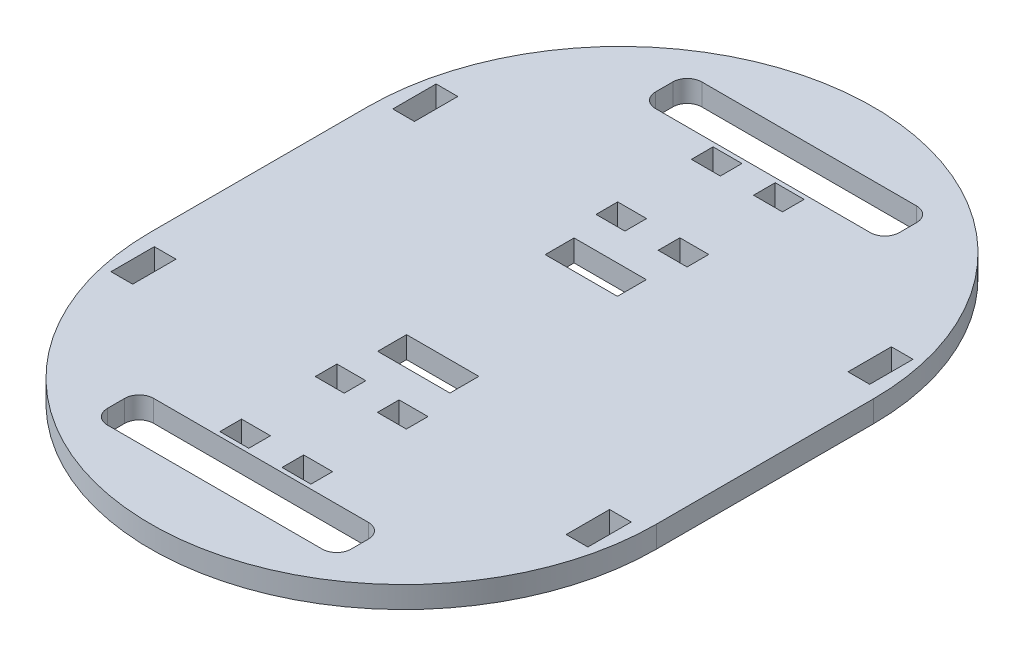
SolidWorks part; units mm, degrees
ref_plane "Front Plane" through (0, 0, 0) normal (0, 0, 1) x (1, 0, 0)
ref_plane "Top Plane" through (0, 0, 0) normal (0, 1, 0) x (1, 0, 0)
ref_plane "Right Plane" through (0, 0, 0) normal (1, 0, 0) x (0, 0, -1)
sketch "Sketch1" plane through (0, 0, 0) normal (0, 1, 0) x (1, 0, 0)
  line L0 (0, 0) -> (0, 76.2) construction
  line L1 (-88.9, 0) -> (-88.9, 76.2)
  line L2 (88.9, 0) -> (88.9, 76.2)
  arc A0 (-88.9, 0) -> (88.9, 0) centre (0, 0) ccw
  arc A1 (88.9, 76.2) -> (-88.9, 76.2) centre (0, 76.2) ccw
  point P3 (0, 38.1)
  dimension "D2" = 88.9
  dimension "D1" = 76.2
extrude "Boss-Extrude1" add sketch "Sketch1" along normal blind 7.62 contours A1 L1 A0 L2
sketch "Sketch2" plane through (0, 7.62, 0) normal (0, 1, 0) x (1, 0, 0)
  line L0 (0, 165.1) -> (0, -88.9) construction
  line L1 (-67.1704, 134.4352) -> (67.1704, 134.4352) construction
  line L3 (-67.1704, -58.2352) -> (67.1704, -58.2352) construction
  line L4 (-42.8387, -66.3632) -> (42.8387, -66.3632)
  line L5 (-42.8387, -66.3632) -> (-42.8387, -50.1072)
  line L6 (-42.8387, -50.1072) -> (42.8387, -50.1072)
  line L7 (42.8387, -66.3632) -> (42.8387, -50.1072)
  line L8 (-42.8387, -66.3632) -> (42.8387, -50.1072) construction
  line L9 (-42.8387, -50.1072) -> (42.8387, -66.3632) construction
  line L15 (-88.9, 38.1) -> (88.9, 38.1) construction
  line L16 (-88.9, 0) -> (-88.9, 76.2) construction
  line L17 (88.9, 0) -> (88.9, 76.2) construction
  line L18 (-42.8387, 142.5632) -> (42.8387, 126.3072) construction
  line L19 (-67.1704, 134.4352) -> (67.1704, 134.4352) construction
  line L20 (-42.8387, 126.3072) -> (42.8387, 142.5632) construction
  line L21 (42.8387, 142.5632) -> (42.8387, 126.3072)
  line L22 (-42.8387, 126.3072) -> (42.8387, 126.3072)
  line L23 (-42.8387, 142.5632) -> (-42.8387, 126.3072)
  line L24 (-42.8387, 142.5632) -> (42.8387, 142.5632)
  arc A0 (88.9, 76.2) -> (-88.9, 76.2) centre (0, 76.2) ccw construction
  arc A1 (-88.9, 0) -> (88.9, 0) centre (0, 0) ccw construction
  point P10 (0, -58.2352)
  dimension "D1" = 16.256
extrude "Cut-Extrude1" cut sketch "Sketch2" against normal through all and the other way through all contours L6 L7 L4 L5 | L22 L21 L24 L23
fillet "Fillet1" radius 5.08 8 edges at (-42.8387, 3.81, -142.5632) (-42.8387, 3.81, -126.3072) (42.8387, 3.81, -142.5632) (42.8387, 3.81, -126.3072) (42.8387, 3.81, 50.1072) (42.8387, 3.81, 66.3632) (-42.8387, 3.81, 66.3632) (-42.8387, 3.81, 50.1072)
sketch "Sketch3" plane through (0, 7.62, 0) normal (0, 1, 0) x (1, 0, 0)
  line L0 (-42.8387, 134.4352) -> (42.8387, 134.4352) construction
  line L1 (-42.8387, 137.4832) -> (-42.8387, 131.3872) construction
  line L2 (42.8387, 137.4832) -> (42.8387, 131.3872) construction
  line L3 (0, 134.4352) -> (0, 83.6352) construction
  line L4 (-16.002, 83.6352) -> (16.002, 83.6352)
  line L5 (16.002, 91.2552) -> (16.002, 134.4352) construction
  line L10 (-16.002, 83.6352) -> (-5.842, 83.6352)
  line L11 (-16.002, 83.6352) -> (-16.002, 91.2552)
  line L12 (-16.002, 91.2552) -> (-5.842, 91.2552)
  line L13 (-5.842, 83.6352) -> (-5.842, 91.2552)
  line L14 (16.002, 83.6352) -> (5.842, 83.6352)
  line L15 (16.002, 83.6352) -> (16.002, 91.2552)
  line L16 (16.002, 91.2552) -> (5.842, 91.2552)
  line L17 (5.842, 83.6352) -> (5.842, 91.2552)
  line L18 (-16.002, 91.2552) -> (-16.002, 134.4352) construction
  line L19 (16.002, 134.4352) -> (16.002, 124.7832) construction
  line L20 (16.002, 117.1632) -> (-16.002, 117.1632) construction
  line L21 (16.002, 124.7832) -> (5.842, 124.7832)
  line L22 (16.002, 124.7832) -> (16.002, 117.1632)
  line L23 (16.002, 117.1632) -> (5.842, 117.1632)
  line L24 (5.842, 124.7832) -> (5.842, 117.1632)
  line L25 (-16.002, 124.7832) -> (-5.842, 124.7832)
  line L26 (-16.002, 124.7832) -> (-16.002, 117.1632)
  line L27 (-16.002, 117.1632) -> (-5.842, 117.1632)
  line L28 (-5.842, 124.7832) -> (-5.842, 117.1632)
  line L29 (-88.9, 38.1) -> (88.9, 38.1) construction
  line L30 (-88.9, 0) -> (-88.9, 76.2) construction
  line L31 (88.9, 0) -> (88.9, 76.2) construction
  line L32 (16.002, -15.0552) -> (5.842, -15.0552)
  line L33 (5.842, -7.4352) -> (5.842, -15.0552)
  line L34 (16.002, -7.4352) -> (5.842, -7.4352)
  line L35 (16.002, -7.4352) -> (16.002, -15.0552)
  line L36 (-16.002, -15.0552) -> (-5.842, -15.0552)
  line L37 (-5.842, -7.4352) -> (-5.842, -15.0552)
  line L38 (-16.002, -7.4352) -> (-5.842, -7.4352)
  line L39 (-16.002, -7.4352) -> (-16.002, -15.0552)
  line L40 (16.002, -40.9632) -> (5.842, -40.9632)
  line L41 (5.842, -48.5832) -> (5.842, -40.9632)
  line L42 (16.002, -48.5832) -> (5.842, -48.5832)
  line L43 (16.002, -48.5832) -> (16.002, -40.9632)
  line L44 (-16.002, -40.9632) -> (-5.842, -40.9632)
  line L45 (-5.842, -48.5832) -> (-5.842, -40.9632)
  line L46 (-16.002, -48.5832) -> (-5.842, -48.5832)
  line L47 (-16.002, -48.5832) -> (-16.002, -40.9632)
  line L48 (42.8387, -58.2352) -> (-42.8387, -58.2352) construction
  line L49 (42.8387, -61.2832) -> (42.8387, -55.1872) construction
  line L50 (-42.8387, -61.2832) -> (-42.8387, -55.1872) construction
  point P12 (0, 83.6352)
  dimension "D1" = 50.8
  dimension "D2" = 32.004
  dimension "D3" = 7.62
  dimension "D4" = 7.62
  dimension "D5" = 9.652
  dimension "D6" = 7.62
  dimension "D7" = 7.62
  dimension "D8" = 0
  dimension "D9" = 9.652
extrude "Cut-Extrude2" cut sketch "Sketch3" against normal through all contours L17 L4 L15 L16 | L4 L13 L12 L11 | L22 L21 L24 L23 | L26 L25 L28 L27 | L36 L37 L38 L39 | L32 L33 L34 L35 | L44 L45 L46 L47 | L40 L41 L42 L43
sketch "Sketch4" plane through (0, 7.62, 0) normal (0, 1, 0) x (1, 0, 0)
  line L0 (-5.842, 83.6352) -> (5.842, 83.6352) construction
  line L1 (5.842, 83.6352) -> (5.842, 73.4752) construction
  line L2 (-12.7, 62.4579) -> (-12.7, 72.6179)
  line L3 (0, 83.6352) -> (0, 67.5379) construction
  line L4 (-12.7, 62.4579) -> (12.7, 62.4579)
  line L5 (-12.7, 72.6179) -> (12.7, 72.6179)
  line L6 (12.7, 62.4579) -> (12.7, 72.6179)
  line L7 (-12.7, 62.4579) -> (12.7, 72.6179) construction
  line L8 (-12.7, 72.6179) -> (12.7, 62.4579) construction
  line L11 (-88.9, 38.1) -> (88.9, 38.1) construction
  line L12 (-88.9, 0) -> (-88.9, 76.2) construction
  line L13 (88.9, 0) -> (88.9, 76.2) construction
  line L14 (-12.7, 13.7421) -> (12.7, 13.7421)
  line L15 (-12.7, 13.7421) -> (-12.7, 3.5821)
  line L16 (-12.7, 3.5821) -> (12.7, 3.5821)
  line L17 (12.7, 13.7421) -> (12.7, 3.5821)
  dimension "D1" = 10.16
  dimension "D2" = 10.16
  dimension "D3" = 25.4
extrude "Cut-Extrude3" cut sketch "Sketch4" against normal through all
sketch "Sketch5" plane through (0, 7.62, 0) normal (0, 1, 0) x (1, 0, 0)
  line L0 (-88.9, 38.1) -> (88.9, 38.1) construction
  line L1 (-88.9, 0) -> (-88.9, 76.2) construction
  line L2 (88.9, 0) -> (88.9, 76.2) construction
  line L3 (0, 165.1) -> (0, -88.9) construction
  line L4 (-83.82, 95.25) -> (-83.82, -19.05) construction
  line L5 (83.82, -3.81) -> (76.2, -3.81)
  line L6 (-83.82, -19.05) -> (-76.2, -19.05)
  line L7 (-83.82, -19.05) -> (-83.82, -3.81)
  line L8 (-83.82, -3.81) -> (-76.2, -3.81)
  line L9 (-76.2, -19.05) -> (-76.2, -3.81)
  line L10 (-83.82, 95.25) -> (-76.2, 95.25)
  line L11 (-83.82, 95.25) -> (-83.82, 80.01)
  line L12 (-83.82, 80.01) -> (-76.2, 80.01)
  line L13 (-76.2, 95.25) -> (-76.2, 80.01)
  line L14 (76.2, -19.05) -> (76.2, -3.81)
  line L15 (83.82, -19.05) -> (76.2, -19.05)
  line L16 (83.82, -19.05) -> (83.82, -3.81)
  line L17 (83.82, 80.01) -> (76.2, 80.01)
  line L18 (76.2, 95.25) -> (76.2, 80.01)
  line L19 (83.82, 95.25) -> (76.2, 95.25)
  line L20 (83.82, 95.25) -> (83.82, 80.01)
  arc A0 (88.9, 76.2) -> (-88.9, 76.2) centre (0, 76.2) ccw construction
  arc A1 (-88.9, 0) -> (88.9, 0) centre (0, 0) ccw construction
  point P16 (-83.82, 38.1)
  dimension "D6" = 7.62
  dimension "D1" = 114.3
  dimension "D2" = 0
  dimension "D3" = 5.08
  dimension "D4" = 15.24
  dimension "D5" = 7.62
  dimension "D7" = 15.24
extrude "Cut-Extrude5" cut sketch "Sketch5" against normal through all
equation "\"D1@Boss-Extrude1\"=\"MDF\""
equation "\"MDF\" = 0.3in"
equation "\"D3@Sketch3\"=\"MDF\""
equation "\"D4@Sketch3\"=\"MDF\""
equation "\"D6@Sketch3\"=\"MDF\""
equation "\"D5@Sketch5\"=\"MDF\""
